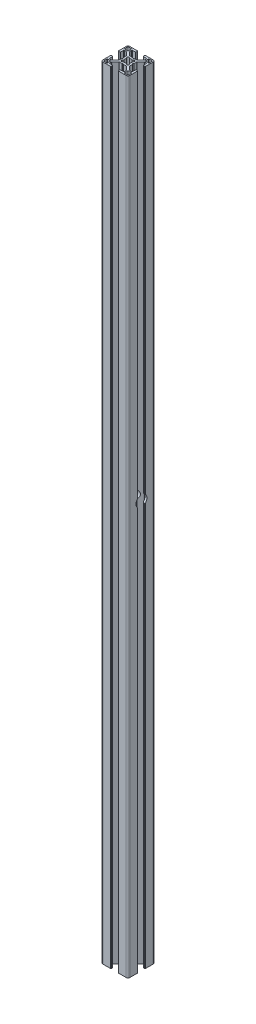
SolidWorks part; units mm, degrees
material "6061 Alloy"
ref_plane "Front Plane" through (0, 0, 0) normal (0, 0, 1) x (1, 0, 0)
ref_plane "Top Plane" through (0, 0, 0) normal (0, 1, 0) x (1, 0, 0)
ref_plane "Right Plane" through (0, 0, 0) normal (1, 0, 0) x (0, 0, -1)
sketch "Sketch1" plane through (0, 0, 0) normal (0, 1, 0) x (1, 0, 0)
  line L0 (296.8106, -41.6994) -> (296.8106, -38.2604)
  line L1 (297.1906, -37.8804) -> (300.6296, -37.8804)
  line L2 (301.0106, -38.2614) -> (301.0106, -41.0804)
  line L3 (300.0106, -42.0804) -> (297.1916, -42.0804)
  line L4 (273.9917, -37.8804) -> (277.4307, -37.8804)
  line L5 (277.8107, -38.2604) -> (277.8107, -41.6994)
  line L6 (277.4297, -42.0804) -> (274.6107, -42.0804)
  line L7 (273.6107, -41.0804) -> (273.6107, -38.2614)
  line L8 (285.8164, -31.5786) -> (284.8373, -32.3604)
  line L9 (283.3307, -30.8538) -> (284.1125, -29.8747)
  line L10 (284.1125, -26.8862) -> (283.3307, -25.9071)
  line L11 (284.8373, -24.4005) -> (285.8164, -25.1823)
  line L12 (288.8049, -25.1823) -> (289.784, -24.4005)
  line L13 (291.2906, -25.9071) -> (290.5088, -26.8862)
  line L14 (290.5088, -29.8747) -> (291.2906, -30.8538)
  line L15 (289.784, -32.3604) -> (288.8049, -31.5786)
  line L16 (277.8107, -15.0615) -> (277.8107, -18.5005)
  line L17 (277.4307, -18.8805) -> (273.9917, -18.8805)
  line L18 (273.6107, -18.4995) -> (273.6107, -15.6805)
  line L19 (274.6107, -14.6805) -> (277.4297, -14.6805)
  line L20 (297.1916, -14.6805) -> (300.0106, -14.6805)
  line L21 (301.0106, -15.6805) -> (301.0106, -18.4995)
  line L22 (300.6296, -18.8805) -> (297.1906, -18.8805)
  line L23 (296.8106, -18.5005) -> (296.8106, -15.0615)
  line L24 (300.0531, -32.8804) -> (300.0531, -36.113)
  line L25 (299.5534, -36.6304) -> (297.5708, -36.6304)
  line L26 (297.2173, -36.484) -> (293.2917, -32.5584)
  line L27 (293.1453, -32.2049) -> (293.1453, -29.3929)
  line L28 (293.1453, -29.3929) -> (292.6353, -28.4429)
  line L29 (292.6353, -28.4429) -> (293.1453, -27.4929)
  line L30 (293.1453, -27.4929) -> (293.1453, -24.556)
  line L31 (293.2917, -24.2024) -> (297.2173, -20.2769)
  line L32 (297.5708, -20.1305) -> (299.5534, -20.1305)
  line L33 (300.0531, -20.6479) -> (300.0531, -23.8804)
  line L34 (300.5531, -24.3804) -> (301.8106, -24.3804)
  line L35 (302.3106, -23.8804) -> (302.3106, -15.3805)
  line L36 (300.3106, -13.3805) -> (291.8106, -13.3805)
  line L37 (291.3106, -13.8805) -> (291.3106, -15.138)
  line L38 (291.8106, -15.638) -> (295.0431, -15.638)
  line L39 (295.5606, -16.1377) -> (295.5606, -18.1203)
  line L40 (295.4142, -18.4738) -> (291.4886, -22.3993)
  line L41 (291.1351, -22.5458) -> (288.2606, -22.5458)
  line L42 (288.2606, -22.5458) -> (287.3106, -23.0558)
  line L43 (287.3106, -23.0558) -> (286.3606, -22.5458)
  line L44 (286.3606, -22.5458) -> (283.4862, -22.5458)
  line L45 (283.1326, -22.3993) -> (279.2071, -18.4738)
  line L46 (279.0607, -18.1203) -> (279.0607, -16.1377)
  line L47 (279.5781, -15.638) -> (282.8106, -15.638)
  line L48 (283.3106, -15.138) -> (283.3106, -13.8805)
  line L49 (282.8106, -13.3805) -> (274.3107, -13.3805)
  line L50 (272.3107, -15.3805) -> (272.3107, -23.8804)
  line L51 (272.8107, -24.3804) -> (274.0682, -24.3804)
  line L52 (274.5682, -23.8804) -> (274.5682, -20.6479)
  line L53 (275.0678, -20.1305) -> (277.0504, -20.1305)
  line L54 (277.404, -20.2769) -> (281.3295, -24.2024)
  line L55 (281.476, -24.556) -> (281.476, -27.4929)
  line L56 (281.476, -27.4929) -> (281.986, -28.4429)
  line L57 (281.986, -28.4429) -> (281.476, -29.3929)
  line L58 (281.476, -29.3929) -> (281.476, -32.2049)
  line L59 (281.3295, -32.5584) -> (277.404, -36.484)
  line L60 (277.0504, -36.6304) -> (275.0678, -36.6304)
  line L61 (274.5682, -36.113) -> (274.5682, -32.8804)
  line L62 (274.0682, -32.3804) -> (272.8107, -32.3804)
  line L63 (272.3107, -32.8804) -> (272.3107, -41.3804)
  line L64 (274.3107, -43.3804) -> (282.8106, -43.3804)
  line L65 (283.3106, -42.8804) -> (283.3106, -41.6229)
  line L66 (282.8106, -41.1229) -> (279.5781, -41.1229)
  line L67 (279.0607, -40.6232) -> (279.0607, -38.6406)
  line L68 (279.2071, -38.2871) -> (283.1326, -34.3616)
  line L69 (283.4862, -34.2151) -> (286.3606, -34.2151)
  line L70 (286.3606, -34.2151) -> (287.3106, -33.7051)
  line L71 (287.3106, -33.7051) -> (288.2606, -34.2151)
  line L72 (288.2606, -34.2151) -> (291.1351, -34.2151)
  line L73 (291.4886, -34.3616) -> (295.4142, -38.2871)
  line L74 (295.5606, -38.6406) -> (295.5606, -40.6232)
  line L75 (295.0431, -41.1229) -> (291.8106, -41.1229)
  line L76 (291.3106, -41.6229) -> (291.3106, -42.8804)
  line L77 (291.8106, -43.3804) -> (300.3106, -43.3804)
  line L78 (302.3106, -41.3804) -> (302.3106, -32.8804)
  line L79 (301.8106, -32.3804) -> (300.5531, -32.3804)
  arc A0 (296.8106, -41.6994) -> (297.1916, -42.0804) centre (297.1916, -41.6994) ccw
  arc A1 (297.1906, -37.8804) -> (296.8106, -38.2604) centre (297.1906, -38.2604) ccw
  arc A2 (301.0106, -38.2614) -> (300.6296, -37.8804) centre (300.6296, -38.2614) ccw
  arc A3 (300.0106, -42.0804) -> (301.0106, -41.0804) centre (300.0106, -41.0804) ccw
  arc A4 (273.9917, -37.8804) -> (273.6107, -38.2614) centre (273.9917, -38.2614) ccw
  arc A5 (277.8107, -38.2604) -> (277.4307, -37.8804) centre (277.4307, -38.2604) ccw
  arc A6 (277.4297, -42.0804) -> (277.8107, -41.6994) centre (277.4297, -41.6994) ccw
  arc A7 (273.6107, -41.0804) -> (274.6107, -42.0804) centre (274.6107, -41.0804) ccw
  arc A8 (285.8164, -31.5786) -> (288.8049, -31.5786) centre (287.3106, -28.3804) ccw
  arc A9 (283.3307, -30.8538) -> (284.8373, -32.3604) centre (284.1684, -31.5227) ccw
  arc A10 (284.1125, -26.8862) -> (284.1125, -29.8747) centre (287.3106, -28.3804) ccw
  arc A11 (284.8373, -24.4005) -> (283.3307, -25.9071) centre (284.1684, -25.2382) ccw
  arc A12 (288.8049, -25.1823) -> (285.8164, -25.1823) centre (287.3106, -28.3804) ccw
  arc A13 (291.2906, -25.9071) -> (289.784, -24.4005) centre (290.4528, -25.2382) ccw
  arc A14 (290.5088, -29.8747) -> (290.5088, -26.8862) centre (287.3106, -28.3804) ccw
  arc A15 (289.784, -32.3604) -> (291.2906, -30.8538) centre (290.4528, -31.5227) ccw
  arc A16 (277.8107, -15.0615) -> (277.4297, -14.6805) centre (277.4297, -15.0615) ccw
  arc A17 (277.4307, -18.8805) -> (277.8107, -18.5005) centre (277.4307, -18.5005) ccw
  arc A18 (273.6107, -18.4995) -> (273.9917, -18.8805) centre (273.9917, -18.4995) ccw
  arc A19 (274.6107, -14.6805) -> (273.6107, -15.6805) centre (274.6107, -15.6805) ccw
  arc A20 (297.1916, -14.6805) -> (296.8106, -15.0615) centre (297.1916, -15.0615) ccw
  arc A21 (301.0106, -15.6805) -> (300.0106, -14.6805) centre (300.0106, -15.6805) ccw
  arc A22 (300.6296, -18.8805) -> (301.0106, -18.4995) centre (300.6296, -18.4995) ccw
  arc A23 (296.8106, -18.5005) -> (297.1906, -18.8805) centre (297.1906, -18.5005) ccw
  arc A24 (300.5531, -32.3804) -> (300.0531, -32.8804) centre (300.5531, -32.8804) ccw
  arc A25 (299.5534, -36.6304) -> (300.0531, -36.113) centre (299.5534, -36.1304) ccw
  arc A26 (297.2173, -36.484) -> (297.5708, -36.6304) centre (297.5708, -36.1304) ccw
  arc A27 (293.1453, -32.2049) -> (293.2917, -32.5584) centre (293.6453, -32.2049) ccw
  arc A28 (293.2917, -24.2024) -> (293.1453, -24.556) centre (293.6453, -24.556) ccw
  arc A29 (297.5708, -20.1305) -> (297.2173, -20.2769) centre (297.5708, -20.6305) ccw
  arc A30 (300.0531, -20.6479) -> (299.5534, -20.1305) centre (299.5534, -20.6305) ccw
  arc A31 (300.0531, -23.8804) -> (300.5531, -24.3804) centre (300.5531, -23.8804) ccw
  arc A32 (301.8106, -24.3804) -> (302.3106, -23.8804) centre (301.8106, -23.8804) ccw
  arc A33 (302.3106, -15.3805) -> (300.3106, -13.3805) centre (300.3106, -15.3805) ccw
  arc A34 (291.8106, -13.3805) -> (291.3106, -13.8805) centre (291.8106, -13.8805) ccw
  arc A35 (291.3106, -15.138) -> (291.8106, -15.638) centre (291.8106, -15.138) ccw
  arc A36 (295.5606, -16.1377) -> (295.0431, -15.638) centre (295.0606, -16.1377) ccw
  arc A37 (295.4142, -18.4738) -> (295.5606, -18.1203) centre (295.0606, -18.1203) ccw
  arc A38 (291.1351, -22.5458) -> (291.4886, -22.3993) centre (291.1351, -22.0458) ccw
  arc A39 (283.1326, -22.3993) -> (283.4862, -22.5458) centre (283.4862, -22.0458) ccw
  arc A40 (279.0607, -18.1203) -> (279.2071, -18.4738) centre (279.5607, -18.1203) ccw
  arc A41 (279.5781, -15.638) -> (279.0607, -16.1377) centre (279.5607, -16.1377) ccw
  arc A42 (282.8106, -15.638) -> (283.3106, -15.138) centre (282.8106, -15.138) ccw
  arc A43 (283.3106, -13.8805) -> (282.8106, -13.3805) centre (282.8106, -13.8805) ccw
  arc A44 (274.3107, -13.3805) -> (272.3107, -15.3805) centre (274.3107, -15.3805) ccw
  arc A45 (272.3107, -23.8804) -> (272.8107, -24.3804) centre (272.8107, -23.8804) ccw
  arc A46 (274.0682, -24.3804) -> (274.5682, -23.8804) centre (274.0682, -23.8804) ccw
  arc A47 (275.0678, -20.1305) -> (274.5682, -20.6479) centre (275.0678, -20.6305) ccw
  arc A48 (277.404, -20.2769) -> (277.0504, -20.1305) centre (277.0504, -20.6305) ccw
  arc A49 (281.476, -24.556) -> (281.3295, -24.2024) centre (280.976, -24.556) ccw
  arc A50 (281.3295, -32.5584) -> (281.476, -32.2049) centre (280.976, -32.2049) ccw
  arc A51 (277.0504, -36.6304) -> (277.404, -36.484) centre (277.0504, -36.1304) ccw
  arc A52 (274.5682, -36.113) -> (275.0678, -36.6304) centre (275.0678, -36.1304) ccw
  arc A53 (274.5682, -32.8804) -> (274.0682, -32.3804) centre (274.0682, -32.8804) ccw
  arc A54 (272.8107, -32.3804) -> (272.3107, -32.8804) centre (272.8107, -32.8804) ccw
  arc A55 (272.3107, -41.3804) -> (274.3107, -43.3804) centre (274.3107, -41.3804) ccw
  arc A56 (282.8106, -43.3804) -> (283.3106, -42.8804) centre (282.8106, -42.8804) ccw
  arc A57 (283.3106, -41.6229) -> (282.8106, -41.1229) centre (282.8106, -41.6229) ccw
  arc A58 (279.0607, -40.6232) -> (279.5781, -41.1229) centre (279.5607, -40.6232) ccw
  arc A59 (279.2071, -38.2871) -> (279.0607, -38.6406) centre (279.5607, -38.6406) ccw
  arc A60 (283.4862, -34.2151) -> (283.1326, -34.3616) centre (283.4862, -34.7151) ccw
  arc A61 (291.4886, -34.3616) -> (291.1351, -34.2151) centre (291.1351, -34.7151) ccw
  arc A62 (295.5606, -38.6406) -> (295.4142, -38.2871) centre (295.0606, -38.6406) ccw
  arc A63 (295.0431, -41.1229) -> (295.5606, -40.6232) centre (295.0606, -40.6232) ccw
  arc A64 (291.8106, -41.1229) -> (291.3106, -41.6229) centre (291.8106, -41.6229) ccw
  arc A65 (291.3106, -42.8804) -> (291.8106, -43.3804) centre (291.8106, -42.8804) ccw
  arc A66 (300.3106, -43.3804) -> (302.3106, -41.3804) centre (300.3106, -41.3804) ccw
  arc A67 (302.3106, -32.8804) -> (301.8106, -32.3804) centre (301.8106, -32.8804) ccw
extrude "Extrude1" add sketch "Sketch1" along normal blind 4000
ref_plane "Plane1" through (293.1453, 4000, 27.4929) normal (0, 0, -1) x (-1, 0, 0)
sketch "Sketch3" plane through (293.1453, 0, 0) normal (1, 0, 0) x (0, 0, -1)
  line L0 (-26.607, -1192.7913) -> (-26.607, 3130) construction
  line L2 (-26.607, -1192.7913) -> (16.1368, -1192.7913) construction
  line L4 (16.1368, -1192.7913) -> (-45.4626, -1192.7913)
  line L5 (16.1368, -1192.7913) -> (16.1368, 3130)
  line L6 (16.1368, 3130) -> (-45.4626, 3130)
  line L7 (-45.4626, -1192.7913) -> (-45.4626, 3130)
extrude "Cut-Extrude3" cut sketch "Sketch3" against normal through all both and the other way through all
ref_plane "Plane2" through (302.3106, 3130, 32.8804) normal (0, 0, 1) x (1, 0, 0)
sketch "Sketch7" plane through (293.1453, 0, 0) normal (1, 0, 0) x (0, 0, -1)
  line L0 (-29.3929, 3130.0099) -> (-29.3929, 3577.0099) construction
  line L1 (-29.3929, 3577.0099) -> (-28.4429, 3577.0099) construction
  line L2 (-26.3267, 3589.2099) -> (-28.4429, 3589.2099) construction
  line L3 (-28.4429, 4000) -> (-28.4429, 3130) construction
  line L4 (-28.4429, 3589.2099) -> (-28.4429, 3577.0099) construction
  line L5 (-29.3929, 4000) -> (-29.3929, 3130) construction
  circle A0 centre (-28.4429, 3583.1099) radius 6.1
  dimension "D1" = 447
  dimension "D2" = 12.2
extrude "Cut-Extrude4" cut sketch "Sketch7" against normal through all both and the other way through all
